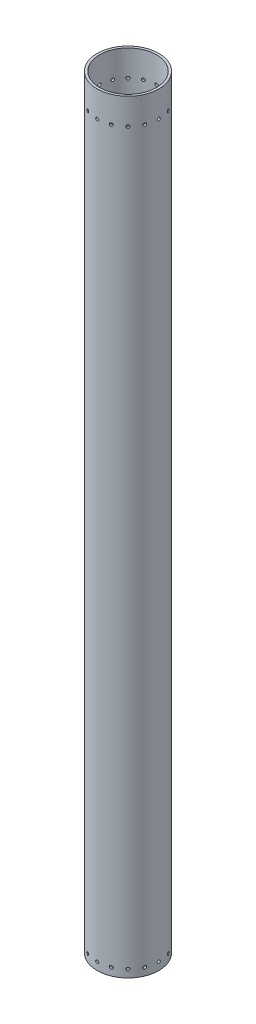
SolidWorks part; units mm, degrees
material "6061-T6 (SS)"
ref_plane "Front Plane" through (0, 0, 0) normal (0, 0, 1) x (1, 0, 0)
ref_plane "Top Plane" through (0, 0, 0) normal (0, 1, 0) x (1, 0, 0)
ref_plane "Right Plane" through (0, 0, 0) normal (1, 0, 0) x (0, 0, -1)
sketch "Sketch1" plane through (0, 0, 0) normal (0, 1, 0) x (1, 0, 0)
  circle A0 centre (0, 0) radius 63.5
  circle A1 centre (0, 0) radius 58.7375
extrude "CasingBody" add sketch "Sketch1" along normal blind 1574.8
ref_plane "HoleFacePlane" through (0, 0, 63.5) normal (0, 0, 1) x (1, 0, 0)
sketch "NozzleReference" plane through (0, 0, 63.5) normal (0, 0, 1) x (1, 0, 0)
  line L0 (-63.5, 0) -> (63.5, 0) construction
  point P4 (0, 15.875)
  dimension "D1" = 15.875
hole_wizard "NozzleHoles" positions "Sketch15" profile "Sketch16" hole size "1/4" standard "ANSI Inch" end condition through all
sketch "Sketch15" plane through (0, 0, 63.5) normal (0, 0, 1) x (1, 0, 0)
  point P0 (0, 15.875)
sketch "Sketch16" plane through (0, 15.875, 63.5) normal (1, 0, 0) x (0, -1, 0)
  line L0 (0, 0) -> (0, 127)
  line L1 (0, 127) -> (3.175, 127)
  line L2 (3.175, 127) -> (3.175, 0)
  line L5 (3.175, 0) -> (0, 0)
  line L11 (0, -6.35) -> (0, 107.95) construction
  dimension "Thru Hole Dia." = 6.35
  dimension "Thru Hole Depth" = 127
sketch "Centerline" plane through (0, 0, 0) normal (0, 0, 1) x (1, 0, 0)
  line L0 (0, 0) -> (0, 1651) construction
pattern_circular "NozzleHolePattern" count 16 over 360 about axis through (0, 0, 0) along (0, 1, 0) of "NozzleHoles"
ref_plane "NozzleReferencePlane" through (0, 15.875, 0) normal (0, 1, 0) x (1, 0, 0)
sketch "ForwardClosureReference" plane through (0, 0, 63.5) normal (0, 0, 1) x (1, 0, 0)
  line L0 (63.5, 1574.8) -> (-63.5, 1574.8) construction
  point P6 (0, 1520.825)
  dimension "D1" = 53.975
ref_plane "ForwardClosureReferencePlane" through (0, 1520.825, 0) normal (0, 1, 0) x (1, 0, 0)
hole_wizard "ClosureHoles" positions "Sketch17" profile "Sketch18" hole size "1/4" standard "ANSI Inch" end condition through all
sketch "Sketch17" plane through (0, 0, 63.5) normal (0, 0, 1) x (1, 0, 0)
  point P0 (0, 1520.825)
sketch "Sketch18" plane through (0, 1520.825, 63.5) normal (1, 0, 0) x (0, -1, 0)
  line L0 (0, 0) -> (0, 127)
  line L1 (0, 127) -> (3.175, 127)
  line L2 (3.175, 127) -> (3.175, 0)
  line L5 (3.175, 0) -> (0, 0)
  line L11 (0, -6.35) -> (0, 107.95) construction
  dimension "Thru Hole Dia." = 6.35
  dimension "Thru Hole Depth" = 127
pattern_circular "ClosureHolePattern" count 16 over 360 about axis through (0, 0, 0) along (0, 1, 0) of "ClosureHoles"
